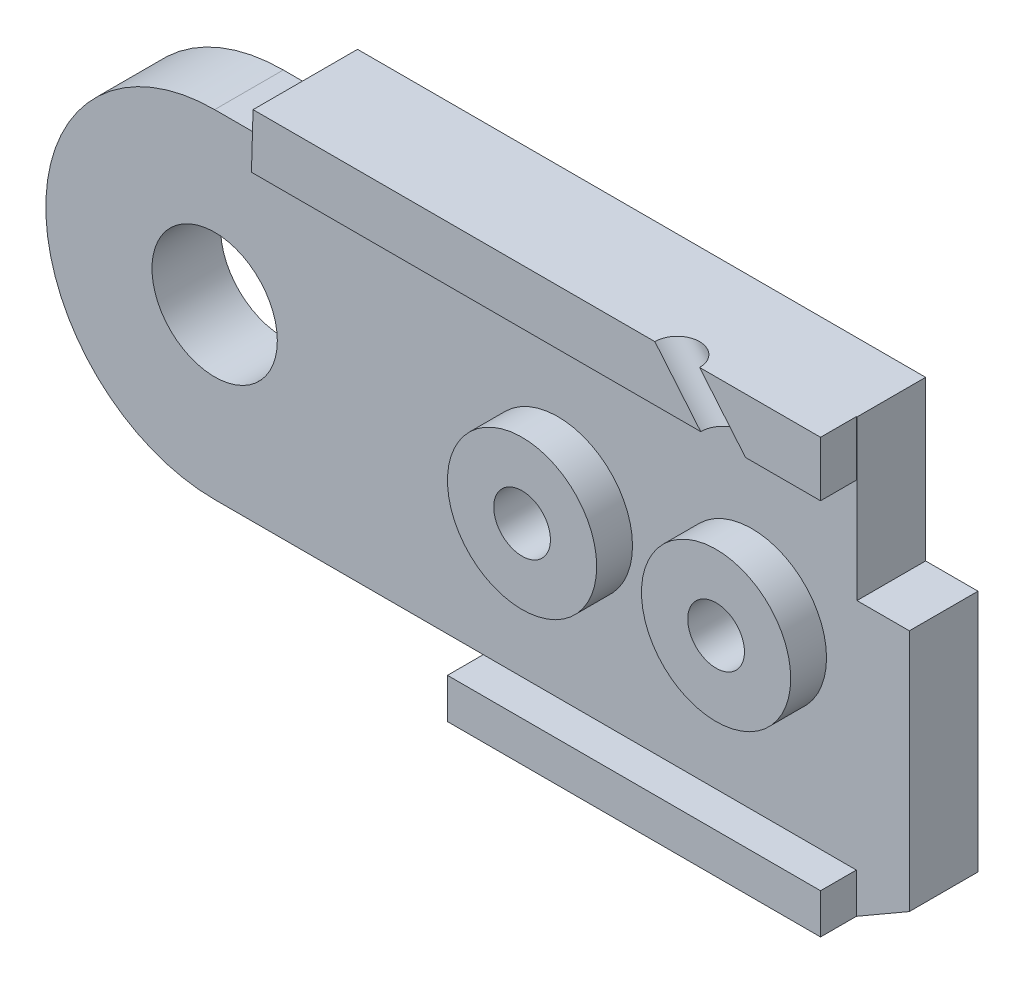
SolidWorks part; units mm, degrees
ref_plane "Front Plane" through (0, 0, 0) normal (0, 0, 1) x (1, 0, 0)
ref_plane "Top Plane" through (0, 0, 0) normal (0, 1, 0) x (1, 0, 0)
ref_plane "Right Plane" through (0, 0, 0) normal (1, 0, 0) x (0, 0, -1)
sketch "Sketch3" plane through (0, 0, 0) normal (0, 0, 1) x (1, 0, 0)
  line L7 (8, 0) -> (9, -2.5)
  line L11 (30, 7) -> (27, 7.5)
  line L13 (0, 7) -> (0, 7.5) construction
  line L14 (0, 7.5) -> (-22.3287, 7.5) construction
  line L15 (0, 5.3) -> (-14, 5.3) construction
  line L16 (0, 4) -> (-14, 4) construction
  line L17 (-14, 4) -> (-14, 5.3) construction
  line L18 (5.6569, 5.6569) -> (5.6569, 7.5)
  line L19 (5.6569, 7.5) -> (27, 7.5)
  line L20 (21.5, -7) -> (9, -7)
  line L21 (9, -7) -> (9, -2.5)
  line L23 (25.0503, -4.9497) -> (21.5, -7)
  arc A4 (8, 0) -> (5.6569, 5.6569) centre (0, 0) ccw
  arc A5 (25.0503, -4.9497) -> (30, 7) centre (30, 0) ccw
  circle A6 centre (0, 0) radius 7 construction
  circle A7 centre (0, 0) radius 3.9 construction
  circle A8 centre (0, 0) radius 5.3 construction
  circle A9 centre (0, 0) radius 4 construction
  dimension "D10" = 0.5
  dimension "D17" = 14
  dimension "D5" = 135
  dimension "D6" = 12.5
  dimension "D7" = 4.5
  dimension "D8" = 1
  dimension "D9" = 45
  dimension "D11" = 1.8431
  dimension "D12" = 30
  dimension "D14" = 3
extrude "Boss-Extrude1" add sketch "Sketch3" along normal blind 2 contours A5 L11 L19 L18 A4 L7 L21 L20 L23
sketch "Sketch20" plane through (0, 0, 0) normal (0, 0, 1) x (1, 0, 0)
  line L0 (0, 7) -> (0, 7.5) construction
  line L1 (0, 7.5) -> (-19.4737, 7.5) construction
  line L2 (0, 5.3) -> (-14, 5.3) construction
  line L3 (0, 4) -> (-14, 4) construction
  line L4 (-14, 4) -> (-14, 5.3) construction
  line L5 (0, 5.3) -> (17.4849, 5.3) construction
  line L6 (17.4849, 5.3) -> (17.4849, 4) construction
  line L7 (17.4849, 4) -> (0, 4) construction
  line L8 (-2.5, 7.5) -> (-2.5, 2.868) construction
  circle A0 centre (0, 0) radius 7 construction
  circle A1 centre (0, 0) radius 3.9 construction
  circle A3 centre (0, 0) radius 5.3 construction
  circle A4 centre (0, 0) radius 4 construction
  circle A5 centre (0, 0) radius 2 construction
  dimension "D1" = 0
  dimension "D2" = 2.5
ref_plane "Plane1" through (0, 0, 2) normal (0, 0, 1) x (1, 0, 0)
sketch "Sketch4" plane through (0, 0, 2) normal (0, 0, 1) x (1, 0, 0)
  line L4 (5.6569, 5.6569) -> (5.6569, 7.5)
  line L5 (5.6569, 5.6569) -> (5.6569, 7.5) construction
  line L6 (5.6569, 7.5) -> (21.5, 7.5)
  line L10 (8, 0) -> (9, -2.5)
  line L11 (9, -2.5) -> (9, -7)
  line L12 (9, -7) -> (21.5, -7)
  line L13 (21.5, -7) -> (21.5, 7.5)
  arc A0 (8, 0) -> (5.6569, 5.6569) centre (0, 0) ccw construction
  arc A3 (8, 0) -> (5.6569, 5.6569) centre (0, 0) ccw
sketch "Sketch22" plane through (0, 0, 2) normal (0, 0, 1) x (1, 0, 0)
  line L0 (5.6569, 5.6569) -> (2.4868, 5.6569)
  line L1 (5.6569, 7.5) -> (21.5, 7.5)
  line L2 (5.6569, 7.5) -> (2.4868, 7.5)
  line L3 (2.4868, 7.5) -> (2.4868, 5.6569)
  line L6 (8, 0) -> (9, -2.5)
  line L7 (9, -2.5) -> (9, -7)
  line L8 (9, -7) -> (21.5, -7)
  line L10 (21.5, 7.5) -> (27, 7.5)
  line L11 (27, 7.5) -> (27, 2.172)
  line L12 (27, 2.172) -> (23.2751, 2.172)
  line L13 (21.5, -7) -> (23.2751, -5.9749)
  line L14 (25.0503, -4.9497) -> (21.5, -7) construction
  line L15 (23.2751, -5.9749) -> (23.2751, 2.172)
  arc A0 (8, 0) -> (5.6569, 5.6569) centre (0, 0) ccw
extrude "Boss-Extrude6" add sketch "Sketch22" along normal blind 2.5
sketch "Sketch25" plane through (0, 0, 2) normal (0, 0, 1) x (1, 0, 0)
  line L0 (0, 5.3) -> (18.0981, 5.3) construction
  line L1 (0, 4) -> (18.0981, 4) construction
  line L2 (18.0981, 4) -> (18.0981, 5.3) construction
sketch "Sketch26" plane through (0, 0, 2) normal (0, 0, 1) x (1, 0, 0)
  line L1 (18.0981, 5.3) -> (2.5301, 5.3)
  line L2 (18.0981, 4) -> (2.5301, 4)
  line L3 (2.5301, 5.3) -> (2.5301, 4)
  line L4 (18.0981, 5.3) -> (27, 5.3)
  line L5 (27, 2.172) -> (27, 7.5) construction
  line L6 (27, 5.3) -> (27, 4)
  line L7 (27, 4) -> (18.0981, 4)
extrude "Cut-Extrude6" cut sketch "Sketch26" along normal blind 2.5
ref_plane "Plane18" through (0, 0, 4.5) normal (0, 0, 1) x (1, 0, 0)
sketch "Sketch31" plane through (0, 0, 4.5) normal (0, 0, 1) x (1, 0, 0)
  line L0 (2.4327, 5.6569) -> (0, 5.6569)
  line L4 (9, -5.6569) -> (0, -5.6569)
  line L5 (2.4327, 5.6569) -> (2.4868, 7.5)
  line L12 (9, -7) -> (9, -5.6569)
  line L13 (9, -2.5) -> (9, -7) construction
  line L16 (27, 7.5) -> (27, 2.172)
  line L17 (27, 2.172) -> (23.2751, 2.172)
  line L18 (23.2751, -5.9749) -> (23.2751, 2.172)
  line L19 (27, 7.5) -> (2.4868, 7.5)
  line L20 (9, -7) -> (21.5, -7)
  line L21 (21.5, -7) -> (23.2751, -5.9749)
  arc A0 (0, 5.6569) -> (0, -5.6569) centre (0, 0) ccw
  dimension "D1" = 5.6569
extrude "Boss-Extrude14" add sketch "Sketch31" along normal blind 2.3 separate body
sketch "Sketch32" plane through (0, 0, 6.8) normal (0, 0, 1) x (1, 0, 0)
  circle A0 centre (0, 0) radius 2.1
extrude "Cut-Extrude7" cut sketch "Sketch32" against normal blind 2.3
sketch "Sketch33" plane through (0, 0, 6.8) normal (0, 0, 1) x (1, 0, 0)
  line L4 (9, -5.6569) -> (9, -7)
  line L11 (9, -7) -> (21.5, -7)
  line L15 (21.5, -7) -> (21.5, -5.6569)
  line L16 (21.5, -5.6569) -> (9, -5.6569)
  line L17 (2.4868, 7.5) -> (21.5, 7.5)
  line L18 (27, 7.5) -> (2.4868, 7.5) construction
  line L19 (2.4868, 7.5) -> (2.4327, 5.6569)
  line L20 (2.4327, 5.6569) -> (21.5, 5.6569)
  line L21 (21.5, 5.6569) -> (21.5, 7.5)
extrude "Boss-Extrude15" add sketch "Sketch33" along normal blind 1.2
sketch "Sketch34" plane through (0, 0, 2) normal (0, 0, 1) x (1, 0, 0)
  line L0 (30, 5.3) -> (18.0981, 5.3) construction
  line L1 (30, 4) -> (18.0981, 4) construction
  circle A0 centre (30, 0) radius 2 construction
  circle A1 centre (30, 0) radius 5.3 construction
  circle A2 centre (30, 0) radius 4 construction
sketch "Sketch35" plane through (0, 0, 6.8) normal (0, 0, 1) x (1, 0, 0)
  line L0 (27, 2.172) -> (27, 7.5)
  line L1 (27, 2.172) -> (21.5204, 2.172)
  line L2 (27, 7.5) -> (21.5204, 7.5)
  line L3 (21.5204, 2.172) -> (21.5204, 7.5)
  line L4 (27, 2.172) -> (27, 7.5) construction
  line L5 (27, 7.5) -> (21.5, 7.5) construction
  dimension "D1" = 0
extrude "Cut-Extrude8" cut sketch "Sketch35" against normal blind 2.4
sketch "Sketch36" plane through (0, 0, 4.4) normal (0, 0, 1) x (1, 0, 0)
  line L0 (27, 2.172) -> (27, 4)
  line L1 (27, 2.172) -> (23.3, 2.172)
  line L2 (27, 4) -> (23.3, 4)
  line L3 (23.3, 2.172) -> (23.3, 4)
  line L4 (21.5, -7) -> (21.5, 7.5) construction
  dimension "D1" = 1.8
extrude "Cut-Extrude9" cut sketch "Sketch36" against normal blind 2.4
sketch "Sketch37" plane through (0, 0, 2) normal (0, 0, 1) x (1, 0, 0)
  circle A0 centre (30, 0) radius 3.9
extrude "Boss-Extrude16" add sketch "Sketch37" along normal blind 2.3
sketch "Sketch39" plane through (0, 0, 4.3) normal (0, 0, 1) x (1, 0, 0)
  line L0 (29, 1.7321) -> (29, -1.7321)
  arc A0 (29, -1.7321) -> (29, 1.7321) centre (30, 0) ccw
  dimension "D2" = 4
  dimension "D1" = 1
extrude "Cut-Extrude10" cut sketch "Sketch39" against normal through all
sketch "Sketch43" plane through (0, 0, 6.8) normal (0, 0, 1) x (1, 0, 0)
  line L2 (0, -5.6569) -> (9, -5.6569) construction
  circle A0 centre (11.5, 0) radius 2.5
  circle A1 centre (18, 0) radius 2.5
  dimension "D1" = 2.5
  dimension "D3" = 5
  dimension "D4" = 6.5
  dimension "D2" = 5.6569
extrude "Boss-Extrude17" add sketch "Sketch43" along normal blind 1.2
sketch "Sketch44" plane through (0, 0, 8) normal (0, 0, 1) x (1, 0, 0)
  circle A0 centre (11.5, 0) radius 0.95
  circle A1 centre (18, 0) radius 0.95
  dimension "D1" = 1.9
  dimension "D2" = 1.9
extrude "Cut-Extrude11" cut sketch "Sketch44" against normal through all
sketch "Sketch45" plane through (0, 0, 0) normal (0, 0, -1) x (-1, 0, 0)
  circle A0 centre (-11.5, 0) radius 2
  circle A1 centre (-18, 0) radius 2
extrude "Cut-Extrude12" cut sketch "Sketch45" against normal blind 2.5
ref_plane "Plane17" through (0, 0, 8) normal (0, 0, 1) x (1, 0, 0)
sketch "Sketch48" plane through (0, 0, 2) normal (0, 0, 1) x (1, 0, 0)
  circle A0 centre (30, 0) radius 5 construction
sketch "Sketch51" plane through (0, 0, 8) normal (0, 0, 1) x (1, 0, 0)
  line L0 (18.2355, 5.6569) -> (27.0112, -4.8677) construction
  line L1 (2.4327, 5.6569) -> (21.5, 5.6569) construction
sketch "Sketch52" plane through (0, 5.6569, 0) normal (0, -1, 0) x (1, 0, 0)
  circle A0 centre (18.2355, 8) radius 0.75
extrude "Cut-Extrude13" cut sketch "Sketch52" along direction (0.6404, -0.768, 0) on the side against the normal blind 10
split "Split1" trim tools "Plane18" bodies to split 129 133 resulting bodies 135 136
delete or keep bodies "Body-Delete/Keep 1" type delete bodies bodies 135
